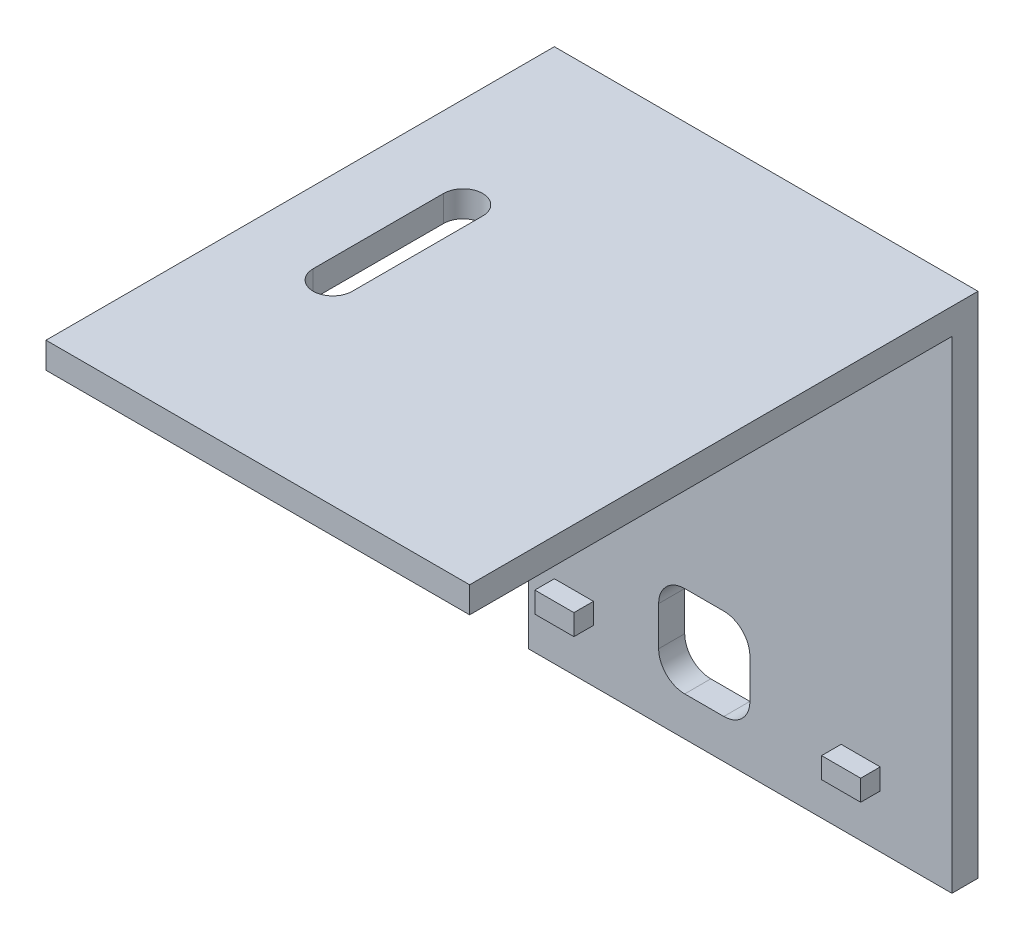
SolidWorks part; units mm, degrees
ref_plane "Front Plane" through (0, 0, 0) normal (0, 0, 1) x (1, 0, 0)
ref_plane "Top Plane" through (0, 0, 0) normal (0, 1, 0) x (1, 0, 0)
ref_plane "Right Plane" through (0, 0, 0) normal (1, 0, 0) x (0, 0, -1)
sketch "Sketch1" plane through (0, 0, 0) normal (0, 0, 1) x (1, 0, 0)
  line L1 (-16.25, -18.5) -> (16.25, -18.5)
  line L2 (-16.25, -18.5) -> (-16.25, 18.5)
  line L3 (-16.25, 18.5) -> (16.25, 18.5)
  line L4 (16.25, -18.5) -> (16.25, 18.5)
  line L5 (-16.25, -18.5) -> (16.25, 18.5) construction
  line L6 (-16.25, 18.5) -> (16.25, -18.5) construction
  point P0 (0, 0)
  dimension "D1" = 32.5
  dimension "D2" = 37
extrude "Boss-Extrude1" add sketch "Sketch1" along normal blind 2
sketch "Sketch2" plane through (0, 0, 2) normal (0, 0, 1) x (1, 0, 0)
  line L0 (-16.25, 18.5) -> (-16.25, -18.5) construction
  line L1 (-14.25, -12.85) -> (-11.25, -12.85)
  line L2 (-14.25, -12.85) -> (-14.25, -14.45)
  line L3 (-14.25, -14.45) -> (-11.25, -14.45)
  line L4 (-11.25, -12.85) -> (-11.25, -14.45)
  line L6 (-14.25, -13.65) -> (19.4094, -13.65) construction
  line L7 (16.25, -18.5) -> (16.25, 18.5) construction
  line L8 (7.75, -14.45) -> (10.75, -14.45)
  line L9 (7.75, -14.45) -> (7.75, -12.85)
  line L10 (7.75, -12.85) -> (10.75, -12.85)
  line L11 (10.75, -14.45) -> (10.75, -12.85)
  line L12 (7.75, -14.45) -> (10.75, -12.85) construction
  line L13 (7.75, -12.85) -> (10.75, -14.45) construction
  line L14 (-16.25, -18.5) -> (16.25, -18.5) construction
  point P10 (9.25, -13.65)
  dimension "D1" = 1.6
  dimension "D2" = 2
  dimension "D3" = 4.05
  dimension "D4" = 3
  dimension "D5" = 5.5
  dimension "D6" = 3
extrude "Boss-Extrude2" add sketch "Sketch2" along normal blind 1.5
sketch "Sketch3" plane through (0, 0, 0) normal (0, 0, -1) x (-1, 0, 0)
  line L0 (6.25, 18.5) -> (6.25, -18.5) construction
  line L1 (-16.25, 18.5) -> (16.25, 18.5) construction
  line L2 (16.25, -18.5) -> (-16.25, -18.5) construction
  line L3 (16.25, 18.5) -> (16.25, -18.5) construction
  line L4 (16.25, -15.5) -> (-16.25, -15.5) construction
  line L5 (-16.25, -18.5) -> (-16.25, 18.5) construction
  line L7 (-0.75, -15.5) -> (6.25, -15.5)
  line L8 (-0.75, -15.5) -> (-0.75, -8.5)
  line L9 (-0.75, -8.5) -> (6.25, -8.5)
  line L10 (6.25, -15.5) -> (6.25, -8.5)
  dimension "D1" = 10
  dimension "D2" = 3
  dimension "D3" = 7
  dimension "D4" = 7
extrude "Cut-Extrude1" cut sketch "Sketch3" against normal through all
fillet "Fillet1" radius 2 4 edges at (-6.25, -15.5, 1) (0.75, -15.5, 1) (-6.25, -8.5, 1) (0.75, -8.5, 1)
sketch "Sketch4" plane through (0, 18.5, 0) normal (0, 1, 0) x (1, 0, 0)
  line L1 (-16.25, 0) -> (16.25, 0)
  line L2 (-16.25, 0) -> (-16.25, -39)
  line L3 (-16.25, -39) -> (16.25, -39)
  line L4 (16.25, 0) -> (16.25, -39)
  dimension "D1" = 39
extrude "Boss-Extrude3" add sketch "Sketch4" along normal blind 2
sketch "Sketch5" plane through (0, 20.5, 0) normal (0, 1, 0) x (1, 0, 0)
  line L0 (-16.25, -24) -> (16.25, -24) construction
  line L1 (-16.25, 0) -> (-16.25, -39) construction
  line L2 (16.25, -39) -> (16.25, 0) construction
  line L3 (-16.25, -39) -> (16.25, -39) construction
  line L4 (-9.25, 0) -> (-9.25, -24) construction
  line L5 (16.25, 0) -> (-16.25, 0) construction
  line L6 (-9.25, -24) -> (-9.25, -14) construction
  line L7 (-10.75, -24) -> (-10.75, -14)
  line L8 (-7.75, -24) -> (-7.75, -14)
  arc A0 (-10.75, -24) -> (-7.75, -24) centre (-9.25, -24) ccw
  arc A1 (-7.75, -14) -> (-10.75, -14) centre (-9.25, -14) ccw
  point P12 (-9.25, -19)
  dimension "D1" = 15
  dimension "D2" = 7
extrude "Cut-Extrude2" cut sketch "Sketch5" against normal blind 2
